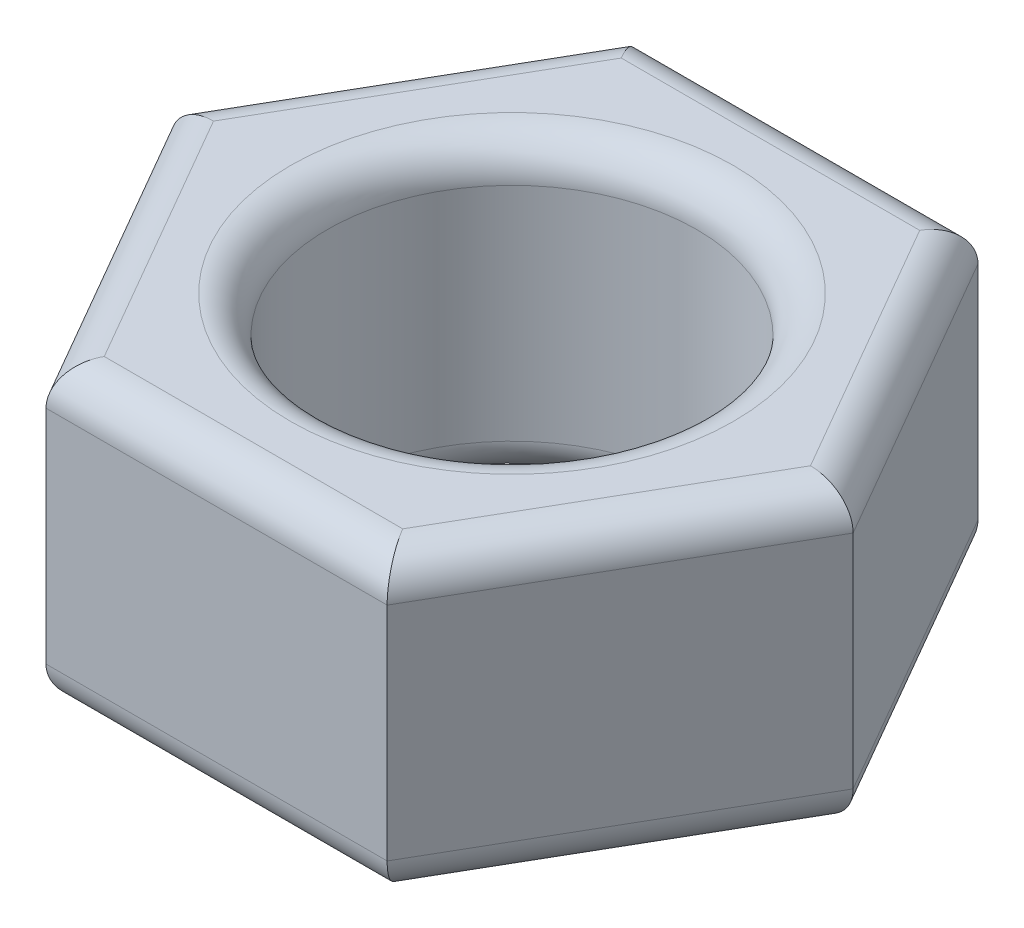
SolidWorks part; units mm, degrees
ref_plane "Front Plane" through (0, 0, 0) normal (0, 0, 1) x (1, 0, 0)
ref_plane "Top Plane" through (0, 0, 0) normal (0, 1, 0) x (1, 0, 0)
ref_plane "Right Plane" through (0, 0, 0) normal (1, 0, 0) x (0, 0, -1)
sketch "Sketch1" plane through (0, 0, 0) normal (0, 1, 0) x (1, 0, 0)
  line L0 (-4.6188, 0) -> (-2.3094, -4)
  line L1 (4.6188, 0) -> (2.3094, 4)
  line L2 (2.3094, 4) -> (-2.3094, 4)
  line L3 (-2.3094, 4) -> (-4.6188, 0)
  line L4 (-2.3094, -4) -> (2.3094, -4)
  line L5 (2.3094, -4) -> (4.6188, 0)
  circle A0 centre (0, 0) radius 4 construction
  circle A1 centre (0, 0) radius 2.5
  dimension "D2" = 5
  dimension "D1" = 8
extrude "Boss-Extrude1" add sketch "Sketch1" along normal blind 4
fillet "Fillet1" radius 0.5 6 edges at (3.4641, 4, 2) (-3.4641, 4, 2) (-3.4641, 4, -2) (3.4641, 4, -2) (0, 4, 4) (0, 4, -4)
fillet "Fillet4" radius 0.5 7 edges at (0, 0, 2.5) (3.4641, 0, -2) (0, 0, -4) (-3.4641, 0, -2) (-3.4641, 0, 2) (0, 0, 4) (3.4641, 0, 2)
fillet "Fillet5" radius 0.5 1 edges at (0, 4, 2.5)
